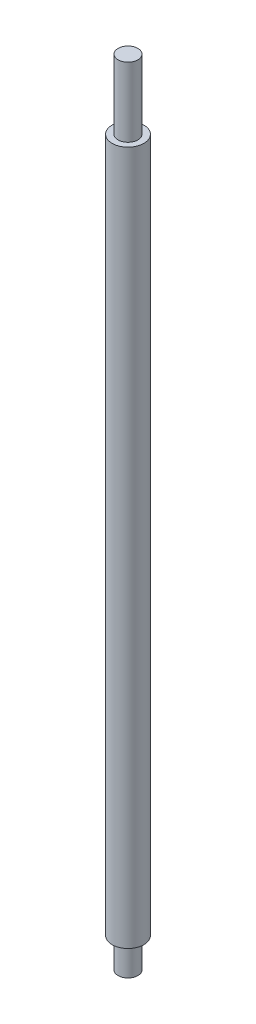
SolidWorks part; units mm, degrees
material "AISI 304"
ref_plane "Front Plane" through (0, 0, 0) normal (0, 0, 1) x (1, 0, 0)
ref_plane "Top Plane" through (0, 0, 0) normal (0, 1, 0) x (1, 0, 0)
ref_plane "Right Plane" through (0, 0, 0) normal (1, 0, 0) x (0, 0, -1)
sketch "Sketch1" plane through (0, 0, 0) normal (0, 1, 0) x (1, 0, 0)
  circle A0 centre (0, 0) radius 8
  dimension "D1" = 16
extrude "Boss-Extrude1" add sketch "Sketch1" along normal blind 350
sketch "Sketch2" plane through (0, 350, 0) normal (0, 1, 0) x (1, 0, 0)
  circle A0 centre (0, 0) radius 5
  dimension "D1" = 10
extrude "Boss-Extrude2" add sketch "Sketch2" along normal blind 35
sketch "Sketch3" plane through (0, 0, 0) normal (0, -1, 0) x (1, 0, 0)
  circle A0 centre (0, 0) radius 5
  dimension "D1" = 10
extrude "Boss-Extrude3" add sketch "Sketch3" along normal blind 15
